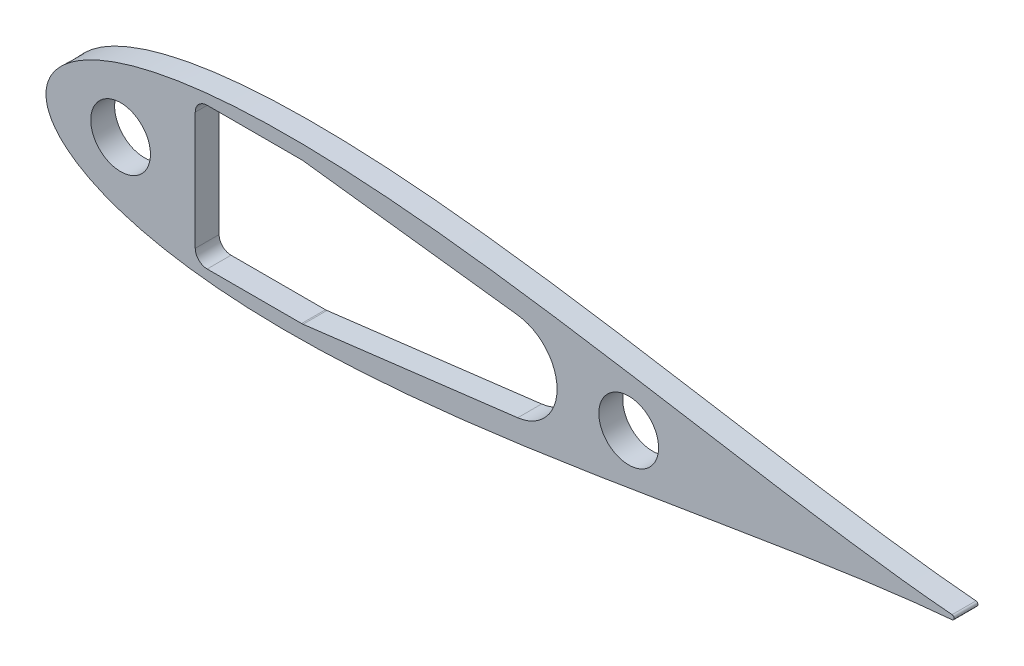
SolidWorks part; units mm, degrees
ref_plane "Front Plane" through (0, 0, 0) normal (0, 0, 1) x (1, 0, 0)
ref_plane "Top Plane" through (0, 0, 0) normal (0, 1, 0) x (1, 0, 0)
ref_plane "Right Plane" through (0, 0, 0) normal (1, 0, 0) x (0, 0, -1)
curve "Curve4"
  spline degree 3 poles (100, 0, 0) (99.8498, 0.0023, 0) (99.4759, 0.008, 0) (99.1023, 0.0238, 0) (98.8789, 0.0332, 0) knots 0 0 0 0 0.401829 1 1 1 1
curve "Curve5"
  spline degree 3 poles (99.3714, -0.0082, 0) (100.2526, 0, 0) (99.3714, 0.0082, 0) (98.8504, 0.035, 0) (97.904, 0.0811, 0) (96.8285, 0.1543, 0) (95.5159, 0.2583, 0) (94.013, 0.3972, 0) (92.313, 0.574, 0) (90.4281, 0.791, 0) (88.3655, 1.0495, 0) (86.1348, 1.3497, 0) (83.7456, 1.691, 0) (81.2082, 2.0715, 0) (78.5335, 2.4886, 0) (75.7326, 2.9386, 0) (72.8172, 3.4168, 0) (69.799, 3.9177, 0) (66.6904, 4.435, 0) (63.5039, 4.9616, 0) (60.2521, 5.4899, 0) (56.948, 6.0119, 0) (53.6049, 6.519, 0) (50.2363, 7.0024, 0) (46.8558, 7.4534, 0) (43.4774, 7.8632, 0) (40.1152, 8.2232, 0) (36.7837, 8.5249, 0) (33.4975, 8.7606, 0) (30.2716, 8.923, 0) (27.1211, 9.0055, 0) (24.0614, 9.0025, 0) (21.108, 8.909, 0) (18.277, 8.7213, 0) (15.5843, 8.4369, 0) (13.0466, 8.0543, 0) (10.6806, 7.5735, 0) (8.5039, 6.996, 0) (6.5349, 6.3253, 0) (4.7933, 5.5673, 0) (3.3001, 4.7321, 0) (2.0777, 3.8366, 0) (1.1467, 2.91, 0) (0.5165, 2.0014, 0) (0.165, 1.1816, 0) (0.0231, 0.524, 0) (-0.0093, 0, 0) (0.0231, -0.524, 0) (0.165, -1.1816, 0) (0.5165, -2.0014, 0) (1.1467, -2.91, 0) (2.0777, -3.8366, 0) (3.3001, -4.7321, 0) (4.7933, -5.5673, 0) (6.5349, -6.3253, 0) (8.5039, -6.996, 0) (10.6806, -7.5735, 0) (13.0466, -8.0543, 0) (15.5843, -8.4369, 0) (18.277, -8.7213, 0) (21.108, -8.909, 0) (24.0614, -9.0025, 0) (27.1211, -9.0055, 0) (30.2716, -8.923, 0) (33.4975, -8.7606, 0) (36.7837, -8.5249, 0) (40.1152, -8.2232, 0) (43.4774, -7.8632, 0) (46.8558, -7.4534, 0) (50.2363, -7.0024, 0) (53.6049, -6.519, 0) (56.948, -6.0119, 0) (60.2521, -5.4899, 0) (63.5039, -4.9616, 0) (66.6904, -4.435, 0) (69.799, -3.9177, 0) (72.8172, -3.4168, 0) (75.7326, -2.9386, 0) (78.5335, -2.4886, 0) (81.2082, -2.0715, 0) (83.7456, -1.691, 0) (86.1348, -1.3497, 0) (88.3655, -1.0495, 0) (90.4281, -0.791, 0) (92.313, -0.574, 0) (94.013, -0.3972, 0) (95.5159, -0.2583, 0) (96.8285, -0.1543, 0) (97.904, -0.0811, 0) (98.8504, -0.035, 0) (99.3714, -0.0082, 0) (100.2526, 0, 0) (99.3714, 0.0082, 0) knots -0.009667 -0.005395 -0.002168 0 0.002168 0.005395 0.009667 0.014967 0.021271 0.028553 0.036781 0.04592 0.055932 0.066773 0.078397 0.090755 0.103793 0.117456 0.131686 0.146422 0.1616 0.177156 0.193024 0.209135 0.225421 0.241812 0.258238 0.274629 0.290914 0.307025 0.322893 0.338448 0.353626 0.368361 0.38259 0.396253 0.40929 0.421647 0.43327 0.444109 0.454119 0.463255 0.471479 0.478755 0.485052 0.490344 0.49461 0.497833 0.5 0.502167 0.50539 0.509656 0.514948 0.521245 0.528521 0.536745 0.545881 0.555891 0.56673 0.578353 0.59071 0.603747 0.61741 0.631639 0.646374 0.661552 0.677107 0.692975 0.709086 0.725371 0.741762 0.758188 0.774579 0.790865 0.806976 0.822844 0.8384 0.853578 0.868314 0.882544 0.896207 0.909245 0.921603 0.933227 0.944068 0.95408 0.963219 0.971447 0.978729 0.985033 0.990333 0.994605 0.997832 1 1.002168 1.005395 1.009667 periodic
sketch "Sketch2" plane through (0, 0, 0) normal (0, 0, 1) x (1, 0, 0)
  line L0 (642.3793, 0) -> (0, 0) construction
  circle A14 centre (642.3793, 0) radius 1.5875 construction
  arc A15 (642.5108, -1.582) -> (642.5108, 1.582) centre (642.3793, 0) ccw
  spline S2 degree 3 poles (666.3448, -0.0547) (672.2538, 0) (666.3448, 0.0547) (662.8509, 0.2344) (656.505, 0.5436) (649.293, 1.0348) (640.4916, 1.7319) (630.4138, 2.6634) (619.0141, 3.8493) (606.375, 5.3044) (592.5439, 7.0376) (577.5855, 9.0506) (561.5643, 11.3389) (544.5497, 13.8907) (526.6141, 16.6877) (507.8326, 19.7051) (488.2827, 22.9117) (468.0444, 26.2704) (447.1994, 29.739) (425.8316, 33.2703) (404.0263, 36.8132) (381.8707, 40.3133) (359.4533, 43.7135) (336.8645, 46.9554) (314.1962, 49.9798) (291.5418, 52.7277) (268.9963, 55.1412) (246.6566, 57.1646) (224.6209, 58.7452) (202.9892, 59.8341) (181.8631, 60.3875) (161.3458, 60.367) (141.542, 59.7399) (122.5581, 58.4818) (104.5023, 56.5743) (87.485, 54.0089) (71.6197, 50.7848) (57.0237, 46.9125) (43.8205, 42.415) (32.1416, 37.3322) (22.1291, 31.7315) (13.9324, 25.7264) (7.6896, 19.5132) (3.4631, 13.4204) (1.1063, 7.9234) (0.1546, 3.5138) (-0.0622, 0) (0.1546, -3.5138) (1.1063, -7.9234) (3.4631, -13.4204) (7.6896, -19.5132) (13.9324, -25.7264) (22.1291, -31.7315) (32.1416, -37.3322) (43.8205, -42.415) (57.0237, -46.9125) (71.6197, -50.7848) (87.485, -54.0089) (104.5023, -56.5743) (122.5581, -58.4818) (141.542, -59.7399) (161.3458, -60.367) (181.8631, -60.3875) (202.9892, -59.8341) (224.6209, -58.7452) (246.6566, -57.1646) (268.9963, -55.1412) (291.5418, -52.7277) (314.1962, -49.9798) (336.8645, -46.9554) (359.4533, -43.7135) (381.8707, -40.3133) (404.0263, -36.8132) (425.8316, -33.2703) (447.1994, -29.739) (468.0444, -26.2704) (488.2827, -22.9117) (507.8326, -19.7051) (526.6141, -16.6877) (544.5497, -13.8907) (561.5643, -11.3389) (577.5855, -9.0506) (592.5439, -7.0376) (606.375, -5.3044) (619.0141, -3.8493) (630.4138, -2.6634) (640.4916, -1.7319) (649.293, -1.0348) (656.505, -0.5436) (662.8509, -0.2344) (666.3448, -0.0547) (672.2538, 0) (666.3448, 0.0547) knots -0.009667 -0.005395 -0.002168 0 0.002168 0.005395 0.009667 0.014967 0.021271 0.028553 0.036781 0.04592 0.055932 0.066773 0.078397 0.090755 0.103793 0.117456 0.131686 0.146422 0.1616 0.177156 0.193024 0.209135 0.225421 0.241812 0.258238 0.274629 0.290914 0.307025 0.322893 0.338448 0.353626 0.368361 0.38259 0.396253 0.40929 0.421647 0.43327 0.444109 0.454119 0.463255 0.471479 0.478755 0.485052 0.490344 0.49461 0.497833 0.5 0.502167 0.50539 0.509656 0.514948 0.521245 0.528521 0.536745 0.545881 0.555891 0.56673 0.578353 0.59071 0.603747 0.61741 0.631639 0.646374 0.661552 0.677107 0.692975 0.709086 0.725371 0.741762 0.758188 0.774579 0.790865 0.806976 0.822844 0.8384 0.853578 0.868314 0.882544 0.896207 0.909245 0.921603 0.933227 0.944068 0.95408 0.963219 0.971447 0.978729 0.985033 0.990333 0.994605 0.997832 1 1.002168 1.005395 1.009667 only from (670.56, 0) to (670.56, 0)
  point P8 (1.2169, -4.6585)
  point P10 (1.2169, 4.6585)
  dimension "D10" = 3.175
extrude "Boss-Extrude1" add sketch "Sketch2" along normal blind 5.4737
extrude "Cut-Extrude4" cut sketch "Sketch7" against normal through all
sketch "Sketch7" plane through (327.9592, -13.7514, 6.35) normal (0, 0, 1) x (1, 0, 0)
  line L1 (-154.9852, -16.7286) -> (-66.0852, -16.7286)
  line L2 (-154.9852, -16.7286) -> (-154.9852, 44.2314)
  line L3 (-154.9852, 44.2314) -> (-66.0852, 44.2314)
  line L4 (-66.0852, -16.7286) -> (-66.0852, 44.2314)
  line L5 (-154.9852, -16.7286) -> (-66.0852, 44.2314) construction
  line L6 (-154.9852, 44.2314) -> (-66.0852, -16.7286) construction
  point P0 (-110.5352, 13.7514)
extrude "Cut-Extrude5" cut sketch "Sketch8" against normal through all
sketch "Sketch8" plane through (327.9592, -13.7514, 6.35) normal (0, 0, 1) x (1, 0, 0)
  circle A0 centre (314.9285, 13.7514) radius 1.2446
scale "Scale1" bodies to scale 101 scale about origin uniform scaling yes scale factor 0.3
sketch "Sketch11" plane through (0, 0, 0) normal (0, 0, -1) x (-1, 0, 0)
  arc A1 (-192.7533, 0.4746) -> (-192.7533, -0.4746) centre (-192.7138, 0) ccw
  arc A2 (-192.7533, 0.4746) -> (-192.7533, -0.4746) centre (-192.7138, 0) ccw
  spline S1 degree 3 poles (1799.3459, -175.6377) (-292.4403, -6.3186) (-236.3918, 3.5698) (-189.1241, -0.799) (-185.7042, -1.1548) (-181.9125, -1.5913) (-177.7632, -2.1113) (-173.2756, -2.7152) (-168.4693, -3.4017) (-163.3649, -4.1672) (-157.9842, -5.0063) (-152.3498, -5.9115) (-146.4848, -6.8735) (-140.4133, -7.8811) (-134.1598, -8.9217) (-127.7495, -9.9811) (-121.2079, -11.044) (-114.5612, -12.094) (-107.836, -13.1141) (-101.0594, -14.0866) (-94.2589, -14.994) (-87.4625, -15.8183) (-80.6989, -16.5424) (-73.997, -17.1494) (-67.3863, -17.6236) (-60.8968, -17.9502) (-54.5589, -18.1163) (-48.4037, -18.1101) (-42.4626, -17.922) (-36.7674, -17.5445) (-31.3507, -16.9723) (-26.2455, -16.2027) (-21.4859, -15.2354) (-17.1071, -14.0738) (-13.1461, -12.7245) (-9.6425, -11.1997) (-6.6387, -9.5194) (-4.1797, -7.7179) (-2.3069, -5.854) (-1.0389, -4.0261) (-0.3319, -2.377) (-0.0464, -1.0541) (0.0186, 0) (-0.0464, 1.0541) (-0.3319, 2.377) (-1.0389, 4.0261) (-2.3069, 5.854) (-4.1797, 7.7179) (-6.6387, 9.5194) (-9.6425, 11.1997) (-13.1461, 12.7245) (-17.1071, 14.0738) (-21.4859, 15.2354) (-26.2455, 16.2027) (-31.3507, 16.9723) (-36.7674, 17.5445) (-42.4626, 17.922) (-48.4037, 18.1101) (-54.5589, 18.1163) (-60.8968, 17.9502) (-67.3863, 17.6236) (-73.997, 17.1494) (-80.6989, 16.5424) (-87.4625, 15.8183) (-94.2589, 14.994) (-101.0594, 14.0866) (-107.836, 13.1141) (-114.5612, 12.094) (-121.2079, 11.044) (-127.7495, 9.9811) (-134.1598, 8.9217) (-140.4133, 7.8811) (-146.4848, 6.8735) (-152.3498, 5.9115) (-157.9842, 5.0063) (-163.3649, 4.1672) (-168.4693, 3.4017) (-173.2756, 2.7152) (-177.7632, 2.1113) (-181.9125, 1.5913) (-185.7042, 1.1548) (-189.1241, 0.799) (-236.3915, -3.5698) (-292.4396, 6.3185) (1799.3062, 175.6345) knots -0.304265 -0.304265 -0.304265 -0.304265 0.021271 0.028553 0.036781 0.04592 0.055932 0.066773 0.078397 0.090755 0.103793 0.117456 0.131686 0.146422 0.1616 0.177156 0.193024 0.209135 0.225421 0.241812 0.258238 0.274629 0.290914 0.307025 0.322893 0.338448 0.353626 0.368361 0.38259 0.396253 0.40929 0.421647 0.43327 0.444109 0.454119 0.463255 0.471479 0.478755 0.485052 0.490344 0.49461 0.497833 0.5 0.502167 0.50539 0.509656 0.514948 0.521245 0.528521 0.536745 0.545881 0.555891 0.56673 0.578353 0.59071 0.603747 0.61741 0.631639 0.646374 0.661552 0.677107 0.692975 0.709086 0.725371 0.741762 0.758188 0.774579 0.790865 0.806976 0.822844 0.8384 0.853578 0.868314 0.882544 0.896207 0.909245 0.921603 0.933227 0.944068 0.95408 0.963219 0.971447 0.978729 1.304263 1.304263 1.304263 1.304263 only from (-192.7533, -0.4746) to (-192.7533, 0.4746)
  spline S2 degree 3 poles (-192.7533, -0.4746) (-192.598, -0.4875) (-191.4281, -0.5861) (-189.1241, -0.799) (-185.7042, -1.1548) (-181.9125, -1.5913) (-177.7632, -2.1113) (-173.2756, -2.7152) (-168.4693, -3.4017) (-163.3649, -4.1672) (-157.9842, -5.0063) (-152.3498, -5.9115) (-146.4848, -6.8735) (-140.4133, -7.8811) (-134.1598, -8.9217) (-127.7495, -9.9811) (-121.2079, -11.044) (-114.5612, -12.094) (-107.836, -13.1141) (-101.0594, -14.0866) (-94.2589, -14.994) (-87.4625, -15.8183) (-80.6989, -16.5424) (-73.997, -17.1494) (-67.3863, -17.6236) (-60.8968, -17.9502) (-54.5589, -18.1163) (-48.4037, -18.1101) (-42.4626, -17.922) (-36.7674, -17.5445) (-31.3507, -16.9723) (-26.2455, -16.2027) (-21.4859, -15.2354) (-17.1071, -14.0738) (-13.1461, -12.7245) (-9.6425, -11.1997) (-6.6387, -9.5194) (-4.1797, -7.7179) (-2.3069, -5.854) (-1.0389, -4.0261) (-0.3319, -2.377) (-0.0464, -1.0541) (0.0186, 0) (-0.0464, 1.0541) (-0.3319, 2.377) (-1.0389, 4.0261) (-2.3069, 5.854) (-4.1797, 7.7179) (-6.6387, 9.5194) (-9.6425, 11.1997) (-13.1461, 12.7245) (-17.1071, 14.0738) (-21.4859, 15.2354) (-26.2455, 16.2027) (-31.3507, 16.9723) (-36.7674, 17.5445) (-42.4626, 17.922) (-48.4037, 18.1101) (-54.5589, 18.1163) (-60.8968, 17.9502) (-67.3863, 17.6236) (-73.997, 17.1494) (-80.6989, 16.5424) (-87.4625, 15.8183) (-94.2589, 14.994) (-101.0594, 14.0866) (-107.836, 13.1141) (-114.5612, 12.094) (-121.2079, 11.044) (-127.7495, 9.9811) (-134.1598, 8.9217) (-140.4133, 7.8811) (-146.4848, 6.8735) (-152.3498, 5.9115) (-157.9842, 5.0063) (-163.3649, 4.1672) (-168.4693, 3.4017) (-173.2756, 2.7152) (-177.7632, 2.1113) (-181.9125, 1.5913) (-185.7042, 1.1548) (-189.1241, 0.799) (-191.4281, 0.5861) (-192.598, 0.4875) (-192.7533, 0.4746) knots 0.020157 0.020157 0.020157 0.020157 0.021271 0.028553 0.036781 0.04592 0.055932 0.066773 0.078397 0.090755 0.103793 0.117456 0.131686 0.146422 0.1616 0.177156 0.193024 0.209135 0.225421 0.241812 0.258238 0.274629 0.290914 0.307025 0.322893 0.338448 0.353626 0.368361 0.38259 0.396253 0.40929 0.421647 0.43327 0.444109 0.454119 0.463255 0.471479 0.478755 0.485052 0.490344 0.49461 0.497833 0.5 0.502167 0.50539 0.509656 0.514948 0.521245 0.528521 0.536745 0.545881 0.555891 0.56673 0.578353 0.59071 0.603747 0.61741 0.631639 0.646374 0.661552 0.677107 0.692975 0.709086 0.725371 0.741762 0.758188 0.774579 0.790865 0.806976 0.822844 0.8384 0.853578 0.868314 0.882544 0.896207 0.909245 0.921603 0.933227 0.944068 0.95408 0.963219 0.971447 0.978729 0.979843 0.979843 0.979843 0.979843
  dimension "D1" = 0
extrude "Boss-Extrude2" add sketch "Sketch11" against normal blind 5.08
sketch "Sketch10" plane through (0, 0, 0) normal (0, 0, 1) x (1, 0, 0)
  line L1 (31.75, -15.0813) -> (56.9172, -15.0813)
  line L2 (31.75, -15.0813) -> (31.75, 15.0812)
  line L3 (31.75, 15.0812) -> (56.9172, 15.0812)
  line L4 (56.9172, -15.0813) -> (56.9172, 15.0812)
  line L5 (31.75, -15.0813) -> (56.9172, 15.0812) construction
  line L6 (31.75, 15.0812) -> (56.9172, -15.0813) construction
  arc A2 (192.7533, -0.4746) -> (192.7533, 0.4746) centre (192.7138, 0) ccw
  arc A3 (192.7533, -0.4746) -> (192.7533, 0.4746) centre (192.7138, 0) ccw construction
  spline S1 degree 3 poles (-802.8924, 93.5757) (271.3771, 3.0555) (227.5753, -2.7549) (189.1241, 0.799) (185.7042, 1.1548) (181.9125, 1.5913) (177.7632, 2.1113) (173.2756, 2.7152) (168.4693, 3.4017) (163.3649, 4.1672) (157.9842, 5.0063) (152.3498, 5.9115) (146.4848, 6.8735) (140.4133, 7.8811) (134.1598, 8.9217) (127.7495, 9.9811) (121.2079, 11.044) (114.5612, 12.094) (107.836, 13.1141) (101.0594, 14.0866) (94.2589, 14.994) (87.4625, 15.8183) (80.6989, 16.5424) (73.997, 17.1494) (67.3863, 17.6236) (60.8968, 17.9502) (54.5589, 18.1163) (48.4037, 18.1101) (42.4626, 17.922) (36.7674, 17.5445) (31.3507, 16.9723) (26.2455, 16.2027) (21.4859, 15.2354) (17.1071, 14.0738) (13.1461, 12.7245) (9.6425, 11.1997) (6.6387, 9.5194) (4.1797, 7.7179) (2.3069, 5.854) (1.0389, 4.0261) (0.3319, 2.377) (0.0464, 1.0541) (-0.0186, 0) (0.0464, -1.0541) (0.3319, -2.377) (1.0389, -4.0261) (2.3069, -5.854) (4.1797, -7.7179) (6.6387, -9.5194) (9.6425, -11.1997) (13.1461, -12.7245) (17.1071, -14.0738) (21.4859, -15.2354) (26.2455, -16.2027) (31.3507, -16.9723) (36.7674, -17.5445) (42.4626, -17.922) (48.4037, -18.1101) (54.5589, -18.1163) (60.8968, -17.9502) (67.3863, -17.6236) (73.997, -17.1494) (80.6989, -16.5424) (87.4625, -15.8183) (94.2589, -14.994) (101.0594, -14.0866) (107.836, -13.1141) (114.5612, -12.094) (121.2079, -11.044) (127.7495, -9.9811) (134.1598, -8.9217) (140.4133, -7.8811) (146.4848, -6.8735) (152.3498, -5.9115) (157.9842, -5.0063) (163.3649, -4.1672) (168.4693, -3.4017) (173.2756, -2.7152) (177.7632, -2.1113) (181.9125, -1.5913) (185.7042, -1.1548) (189.1241, -0.799) (227.5741, 2.7548) (271.3742, -3.0552) (-802.7842, -93.5666) knots -0.240652 -0.240652 -0.240652 -0.240652 0.021271 0.028553 0.036781 0.04592 0.055932 0.066773 0.078397 0.090755 0.103793 0.117456 0.131686 0.146422 0.1616 0.177156 0.193024 0.209135 0.225421 0.241812 0.258238 0.274629 0.290914 0.307025 0.322893 0.338448 0.353626 0.368361 0.38259 0.396253 0.40929 0.421647 0.43327 0.444109 0.454119 0.463255 0.471479 0.478755 0.485052 0.490344 0.49461 0.497833 0.5 0.502167 0.50539 0.509656 0.514948 0.521245 0.528521 0.536745 0.545881 0.555891 0.56673 0.578353 0.59071 0.603747 0.61741 0.631639 0.646374 0.661552 0.677107 0.692975 0.709086 0.725371 0.741762 0.758188 0.774579 0.790865 0.806976 0.822844 0.8384 0.853578 0.868314 0.882544 0.896207 0.909245 0.921603 0.933227 0.944068 0.95408 0.963219 0.971447 0.978729 1.240643 1.240643 1.240643 1.240643 only from (192.7533, 0.4746) to (192.7533, -0.4746)
  point P0 (44.3336, 0)
  dimension "D1" = 25.1672
  dimension "D2" = 31.75
  dimension "D5" = 30.1625
  dimension "D3" = 0
extrude "Cut-Extrude6" cut sketch "Sketch10" along normal through all
fillet "Fillet1" radius 2.54 4 edges at (56.9172, -15.0813, 2.54) (31.75, -15.0813, 2.54) (31.75, 15.0812, 2.54) (56.9172, 15.0812, 2.54)
hole_wizard "#8 Clearance Hole1" positions "Sketch12" profile "Sketch13" hole size "#8" standard "ANSI Inch"
sketch "Sketch12" plane through (0, 0, 5.08) normal (0, 0, 1) x (1, 0, 0)
  line L0 (76.2, 0) -> (0, 0) construction
  line L2 (31.75, 8.8646) -> (31.75, -8.8646) construction
  point P0 (12.7, 0)
  point P2 (76.2, 0)
  dimension "D1" = 19.05
  dimension "D2" = 44.45
sketch "Sketch13" plane through (12.7, 0, 5.08) normal (1, 0, 0) x (0, -1, 0)
  line L0 (0, 0) -> (0, 5.08)
  line L1 (0, 5.08) -> (2.2479, 5.08)
  line L2 (2.2479, 5.08) -> (2.2479, 0)
  line L5 (2.2479, 0) -> (0, 0)
  line L11 (0, -6.35) -> (0, 107.95) construction
  dimension "Thru Hole Dia." = 4.4958
  dimension "Thru Hole Depth" = 5.08
sketch "Sketch15" plane through (0, 0, 5.08) normal (0, 0, 1) x (1, 0, 0)
  line L0 (32.4939, 14.3373) -> (56.1732, -14.3373)
  line L1 (20.8929, 12.7) -> (71.6929, -12.7) construction
  line L2 (23.4329, 12.7) -> (69.1529, 12.7)
  line L3 (20.8929, 10.16) -> (20.8929, -10.16)
  line L4 (23.4329, -12.7) -> (69.1529, -12.7)
  line L5 (71.6929, 10.16) -> (71.6929, -10.16)
  circle A0 centre (44.3336, 0) radius 13.716
  arc A1 (34.29, 15.0812) -> (31.75, 12.5412) centre (34.29, 12.5412) ccw construction
  arc A2 (54.3772, -15.0813) -> (56.9172, -12.5412) centre (54.3772, -12.5412) ccw construction
  arc A3 (69.1529, 12.7) -> (71.6929, 10.16) centre (69.1529, 10.16) cw
  arc A4 (71.6929, -10.16) -> (69.1529, -12.7) centre (69.1529, -10.16) cw
  arc A5 (23.4329, -12.7) -> (20.8929, -10.16) centre (23.4329, -10.16) cw
  arc A6 (23.4329, 12.7) -> (20.8929, 10.16) centre (23.4329, 10.16) ccw
  point P10 (46.2929, 0)
  point P18 (71.6929, 12.7)
  dimension "D1" = 27.432
  dimension "D4" = 2.54
  dimension "D2" = 50.8
  dimension "D3" = 25.4
sketch "Sketch16" plane through (0, 0, 5.08) normal (0, 0, 1) x (1, 0, 0)
  line L0 (99.1976, 0) -> (97.4196, 0) construction
  line L1 (99.1976, -9.525) -> (97.4196, -9.525)
  line L2 (99.1976, 9.525) -> (97.4196, 9.525)
  arc A0 (99.1976, -9.525) -> (99.1976, 9.525) centre (99.1976, 0) ccw
  arc A1 (97.4196, 9.525) -> (97.4196, -9.525) centre (97.4196, 0) ccw
  point P3 (98.3086, 0)
  dimension "D1" = 9.525
  dimension "D2" = 1.778
  dimension "D3" = 53.975
extrude "Cut-Extrude8" cut sketch "Sketch16" against normal through all
sketch "Sketch18" plane through (0, 0, 5.08) normal (0, 0, 1) x (1, 0, 0)
  line L2 (54.6867, 15.0623) -> (100.3585, 9.454)
  line L4 (100.3585, -9.454) -> (54.6867, -15.0623)
  line L5 (56.9172, -12.5412) -> (56.9172, 12.5412) construction
  line L8 (56.9172, -12.5412) -> (56.9172, 12.5412)
  arc A0 (56.9172, 12.5412) -> (54.3772, 15.0812) centre (54.3772, 12.5412) ccw construction
  arc A3 (99.1976, -9.525) -> (99.1976, 9.525) centre (99.1976, 0) ccw construction
  arc A4 (54.3772, -15.0813) -> (56.9172, -12.5412) centre (54.3772, -12.5412) ccw construction
  arc A6 (100.3585, -9.454) -> (100.3585, 9.454) centre (99.1976, 0) ccw
  arc A8 (54.6867, -15.0623) -> (56.9172, -12.5412) centre (54.3772, -12.5412) ccw
  arc A9 (56.9172, 12.5412) -> (54.6867, 15.0623) centre (54.3772, 12.5412) ccw
extrude "Cut-Extrude9" cut sketch "Sketch18" against normal through all
sketch "Sketch19" plane through (0, 0, 5.08) normal (0, 0, 1) x (1, 0, 0)
  line L0 (0, 0) -> (108.7226, 0) construction
  line L1 (31.75, 12.5412) -> (31.75, -12.5412) construction
  circle A0 centre (15.875, 0) radius 6.35
  circle A1 centre (123.9626, 0) radius 6.35
  arc A2 (100.3585, -9.454) -> (100.3585, 9.454) centre (99.1976, 0) ccw construction
  point P10 (15.7526, 0)
  point P11 (91.9738, 0)
  point P12 (124.3268, 0)
  dimension "D1" = 12.7
  dimension "D2" = 12.7
  dimension "D3" = 15.24
  dimension "D4" = 15.875
extrude "Cut-Extrude10" cut sketch "Sketch19" against normal through all
equation "\"0.5n\"=0"
equation "\"D1@Sketch10\"=0.898/cos(25deg)"
